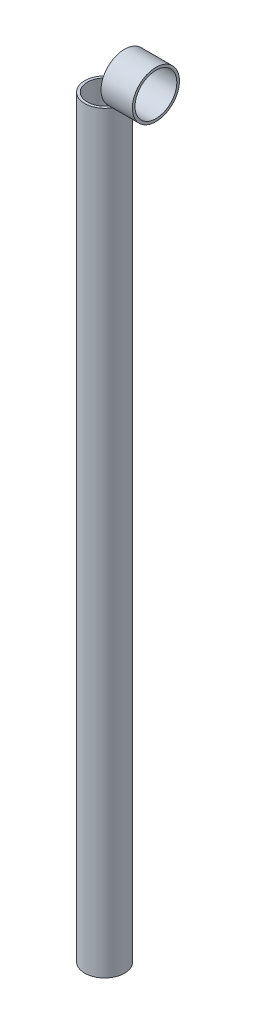
SolidWorks part; units mm, degrees
ref_plane "Front Plane" through (0, 0, 0) normal (0, 0, 1) x (1, 0, 0)
ref_plane "Top Plane" through (0, 0, 0) normal (0, 1, 0) x (1, 0, 0)
ref_plane "Right Plane" through (0, 0, 0) normal (1, 0, 0) x (0, 0, -1)
sketch "Sketch1" plane through (0, 0, 0) normal (0, 1, 0) x (1, 0, 0)
  circle A0 centre (0, 0) radius 24.13
  circle A1 centre (0, 0) radius 20.955
  dimension "D1" = 3.175
  dimension "D2" = 48.26
extrude "Boss-Extrude1" add sketch "Sketch1" along normal blind 914.4
sketch "Sketch2" plane through (0, 0, 0) normal (1, 0, 0) x (0, 0, -1)
  line L1 (24.13, 914.4) -> (-24.13, 914.4) construction
  circle A0 centre (0, 942.975) radius 28.575
  circle A1 centre (0, 942.975) radius 25.4
  dimension "D1" = 57.15
  dimension "D2" = 3.175
extrude "Boss-Extrude2" add sketch "Sketch2" along normal blind 38.1 from offset 24.13 separate body
